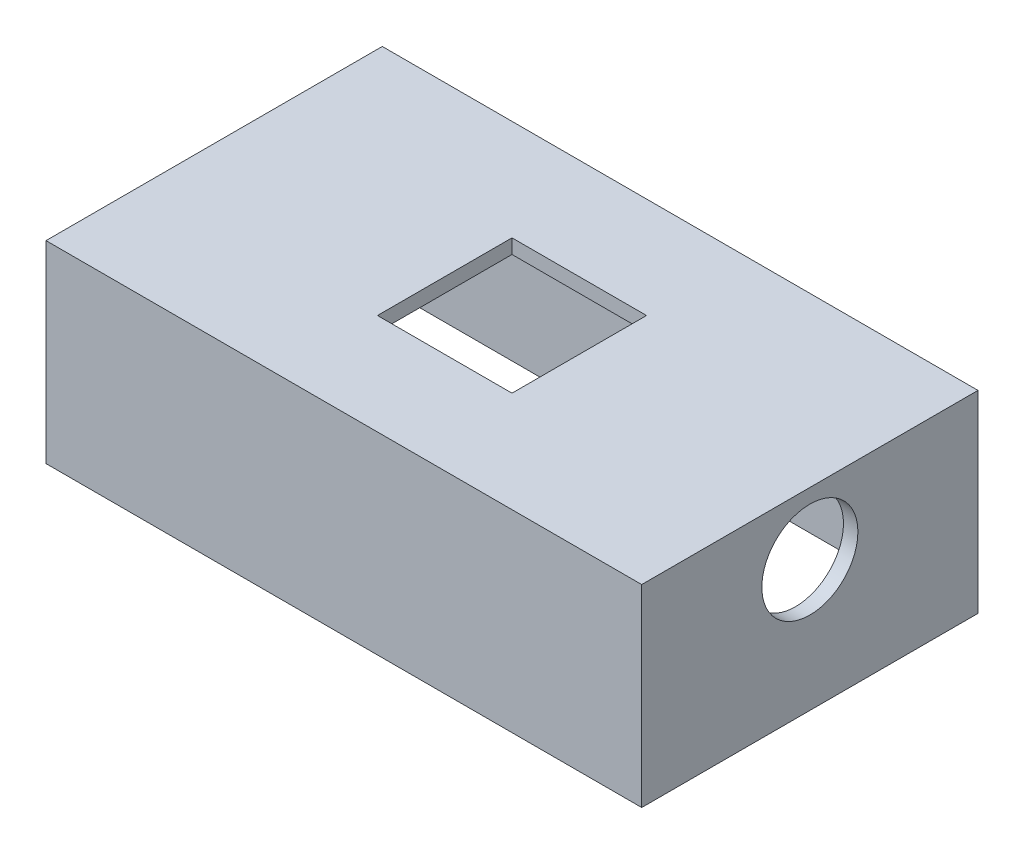
SolidWorks part; units mm, degrees
material "ABS PC"
ref_plane "前视基准面" through (0, 0, 0) normal (0, 0, 1) x (1, 0, 0)
ref_plane "上视基准面" through (0, 0, 0) normal (0, 1, 0) x (1, 0, 0)
ref_plane "右视基准面" through (0, 0, 0) normal (1, 0, 0) x (0, 0, -1)
sketch "草图1" plane through (0, 0, 0) normal (0, 1, 0) x (1, 0, 0)
  line L1 (-28.0032, 22.2518) -> (33.9968, 22.2518)
  line L2 (-28.0032, 22.2518) -> (-28.0032, -12.7482)
  line L3 (-28.0032, -12.7482) -> (33.9968, -12.7482)
  line L4 (33.9968, 22.2518) -> (33.9968, -12.7482)
  dimension "D1" = 35
  dimension "D2" = 62
extrude "凸台-拉伸1" add sketch "草图1" along normal blind 1.5
sketch "草图2" plane through (0, 0, 0) normal (0, -1, 0) x (1, 0, 0)
  line L0 (-28.0032, 12.7482) -> (33.9968, 12.7482) construction
  line L1 (-28.0032, 12.7482) -> (33.9968, 12.7482)
  line L2 (-28.0032, -22.2518) -> (-28.0032, 12.7482) construction
  line L3 (-28.0032, -22.2518) -> (-28.0032, 12.7482)
  line L4 (33.9968, -22.2518) -> (-28.0032, -22.2518) construction
  line L5 (33.9968, -22.2518) -> (-28.0032, -22.2518)
  line L6 (33.9968, 12.7482) -> (33.9968, -22.2518) construction
  line L7 (33.9968, 12.7482) -> (33.9968, -22.2518)
extrude "凸台-拉伸2" add sketch "草图2" along normal up to surface (16.1 mm away)
sketch "草图3" plane through (0, -16.1, 0) normal (0, -1, 0) x (1, 0, 0)
  line L0 (32.4968, -20.7518) -> (32.4968, 11.2482) construction
  line L1 (-26.5032, -20.7518) -> (32.4968, -20.7518) construction
  line L2 (-26.5032, 11.2482) -> (-26.5032, -20.7518) construction
  line L3 (32.4968, 11.2482) -> (-26.5032, 11.2482) construction
  line L4 (32.4968, -20.7518) -> (32.4968, 11.2482)
  line L5 (-26.5032, -20.7518) -> (32.4968, -20.7518)
  line L6 (-26.5032, 11.2482) -> (-26.5032, -20.7518)
  line L7 (32.4968, 11.2482) -> (-26.5032, 11.2482)
extrude "切除-拉伸1" cut sketch "草图3" against normal blind 41
sketch "草图4" plane through (0, 1.5, 0) normal (0, 1, 0) x (1, 0, 0)
  line L0 (-28.0032, -12.7482) -> (33.9968, -12.7482) construction
  line L1 (-26.5032, -11.2482) -> (32.4968, -11.2482) construction
  line L2 (32.4968, -11.2482) -> (32.4968, 20.7518) construction
  line L3 (33.9968, -12.7482) -> (33.9968, 22.2518) construction
  line L4 (32.4968, 20.7518) -> (-26.5032, 20.7518) construction
  line L5 (33.9968, 22.2518) -> (-28.0032, 22.2518) construction
  line L6 (-28.0032, 22.2518) -> (-28.0032, -12.7482) construction
  line L7 (-26.5032, 20.7518) -> (-26.5032, -11.2482) construction
  line L8 (-28.0032, -12.7482) -> (33.9968, -12.7482)
  line L9 (-26.5032, -11.2482) -> (32.4968, -11.2482)
  line L10 (32.4968, -11.2482) -> (32.4968, 20.7518)
  line L11 (33.9968, -12.7482) -> (33.9968, 22.2518)
  line L12 (32.4968, 20.7518) -> (-26.5032, 20.7518)
  line L13 (33.9968, 22.2518) -> (-28.0032, 22.2518)
  line L14 (-28.0032, 22.2518) -> (-28.0032, -12.7482)
  line L15 (-26.5032, 20.7518) -> (-26.5032, -11.2482)
extrude "凸台-拉伸3" add sketch "草图4" along normal blind 1
sketch "草图5" plane through (0, 2.5, 0) normal (0, 1, 0) x (1, 0, 0)
  line L0 (33.9968, -12.7482) -> (33.9968, 22.2518) construction
  line L1 (-28.0032, -12.7482) -> (33.9968, -12.7482) construction
  line L2 (-28.0032, 22.2518) -> (-28.0032, -12.7482) construction
  line L3 (33.9968, 22.2518) -> (-28.0032, 22.2518) construction
  line L4 (33.9968, -12.7482) -> (33.9968, 22.2518)
  line L5 (-28.0032, -12.7482) -> (33.9968, -12.7482)
  line L6 (-28.0032, 22.2518) -> (-28.0032, -12.7482)
  line L7 (33.9968, 22.2518) -> (-28.0032, 22.2518)
extrude "凸台-拉伸4" add sketch "草图5" along normal blind 1.5
sketch "草图8" plane through (33.9968, 0, 0) normal (1, 0, 0) x (0, 0, -1)
  line L0 (-12.7482, 4) -> (22.2518, 4) construction
  line L1 (22.2518, 4) -> (22.2518, -16.1) construction
  line L2 (-12.7482, 4) -> (-12.7482, -16.1) construction
  circle A0 centre (4.7518, -2.5) radius 5
  dimension "D1" = 10
  dimension "D2" = 6.5
  dimension "D3" = 17.5
  dimension "D4" = 17.5
extrude "切除-拉伸3" cut sketch "草图8" against normal blind 1.5
sketch "草图10" plane through (0, 4, 0) normal (0, 1, 0) x (1, 0, 0)
  line L1 (-4.0032, 11.7518) -> (9.9968, 11.7518)
  line L2 (-4.0032, 11.7518) -> (-4.0032, -2.2482)
  line L3 (-4.0032, -2.2482) -> (9.9968, -2.2482)
  line L4 (9.9968, 11.7518) -> (9.9968, -2.2482)
  line L5 (33.9968, 22.2518) -> (-28.0032, 22.2518) construction
  line L6 (-28.0032, -12.7482) -> (33.9968, -12.7482) construction
  line L7 (-28.0032, 22.2518) -> (-28.0032, -12.7482) construction
  line L8 (33.9968, -12.7482) -> (33.9968, 22.2518) construction
  dimension "D1" = 14
  dimension "D2" = 14
  dimension "D3" = 10.5
  dimension "D4" = 10.5
  dimension "D5" = 24
  dimension "D6" = 24
extrude "切除-拉伸4" cut sketch "草图10" against normal up to next
